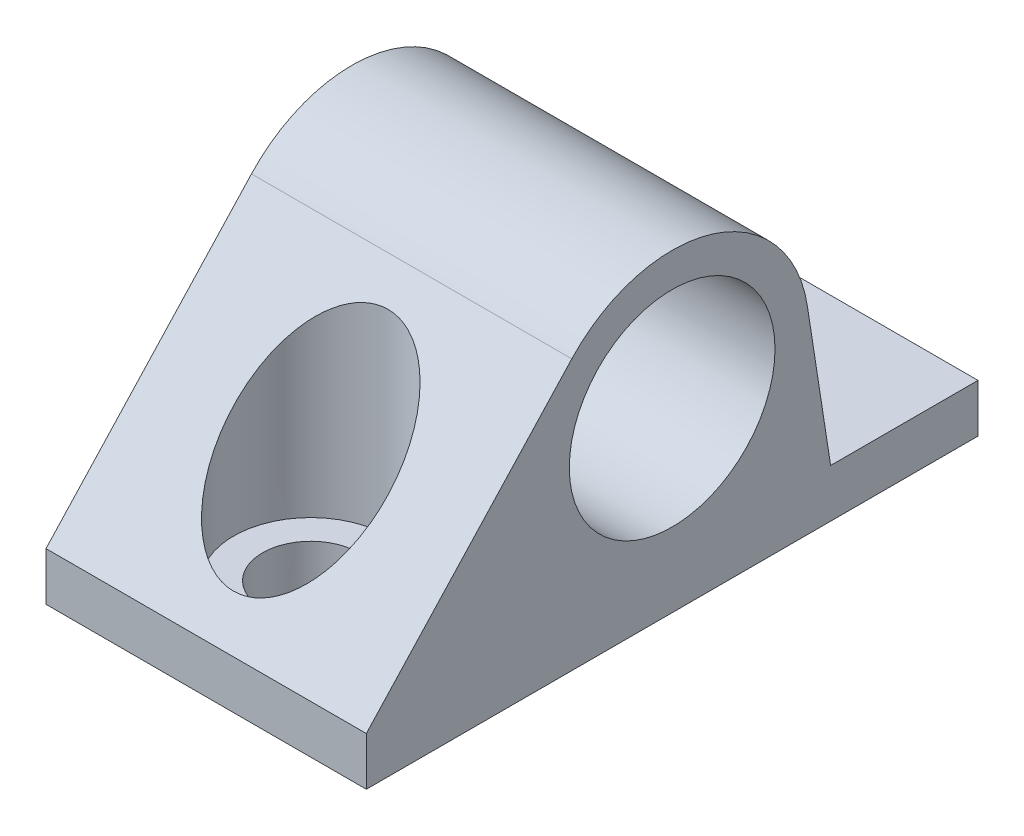
SolidWorks part; units mm, degrees
material "ABS"
ref_plane "Front Plane" through (0, 0, 0) normal (0, 0, 1) x (1, 0, 0)
ref_plane "Top Plane" through (0, 0, 0) normal (0, 1, 0) x (1, 0, 0)
ref_plane "Right Plane" through (0, 0, 0) normal (1, 0, 0) x (0, 0, -1)
sketch "Sketch1" plane through (0, 0, 0) normal (0, 0, 1) x (1, 0, 0)
  line L0 (101.6062, 195.4843) -> (108.5162, 195.4843)
  line L1 (114.6049, 195.4843) -> (108.5162, 195.4843)
  line L4 (114.6049, 195.4843) -> (121.5062, 195.4843)
  line L5 (121.5062, 195.4843) -> (121.5062, 198.4843)
  line L6 (121.5062, 198.4843) -> (101.6062, 198.4843)
  line L7 (101.6062, 198.4843) -> (101.6062, 195.4843)
  dimension "D1" = 3
  dimension "D3" = 19.9
  dimension "D4" = 6.91
extrude "Boss-Extrude1" add sketch "Sketch1" against normal blind 38
sketch "Sketch2" plane through (101.6062, 0, 0) normal (-1, 0, 0) x (0, 0, 1)
  line L0 (-28.844, 198.4843) -> (-27.3994, 207.7884)
  line L1 (-38, 198.4843) -> (0, 198.4843) construction
  line L2 (-12.7649, 212.2613) -> (0, 198.4843)
  line L3 (0, 198.4843) -> (-28.844, 198.4843)
  line L4 (-19, 198.4843) -> (-19, 206.4843) construction
  line L5 (0, 198.4843) -> (0, 195.4843) construction
  arc A0 (-27.3994, 207.7884) -> (-12.7649, 212.2613) centre (-19, 206.4843) cw
  circle A1 centre (-19, 206.4843) radius 6.39
  dimension "D2" = 8.5
  dimension "D3" = 12.78
  dimension "D1" = 8
  dimension "D4" = 19
extrude "Boss-Extrude2" add sketch "Sketch2" against normal up to vertex (19.9 mm away) up to point (121.5062, 198.4843, -38)
ref_plane "Plane1" through (111.5562, 0, 0) normal (-1, 0, 0) x (0, 0, 1)
sketch "Sketch3" plane through (111.5562, 0, 0) normal (-1, 0, 0) x (0, 0, 1)
  line L0 (-26.7, 211.67) -> (-26.7, 198.4843)
  line L1 (-26.7, 198.4843) -> (-28.5, 198.4843)
  line L2 (-28.5, 198.4843) -> (-28.5, 189.9061)
  line L3 (-28.5, 189.9061) -> (-31.5, 189.9061)
  line L4 (-31.5, 189.9061) -> (-31.5, 211.67)
  line L5 (-31.5, 211.67) -> (-26.7, 211.67)
  line L6 (-38, 198.4843) -> (-38, 195.4843) construction
  dimension "D1" = 4.8
  dimension "D2" = 3
  dimension "D3" = 3
  dimension "D4" = 6.5
revolve "Cut-Revolve1" cut sketch "Sketch3" angle 360 about L4
ref_plane "Plane2" through (0, 0, -19) normal (0, 0, -1) x (-1, 0, 0)
mirror "Mirror1" about plane through (0, 0, -19) normal (0, 0, -1) of "Cut-Revolve1"
